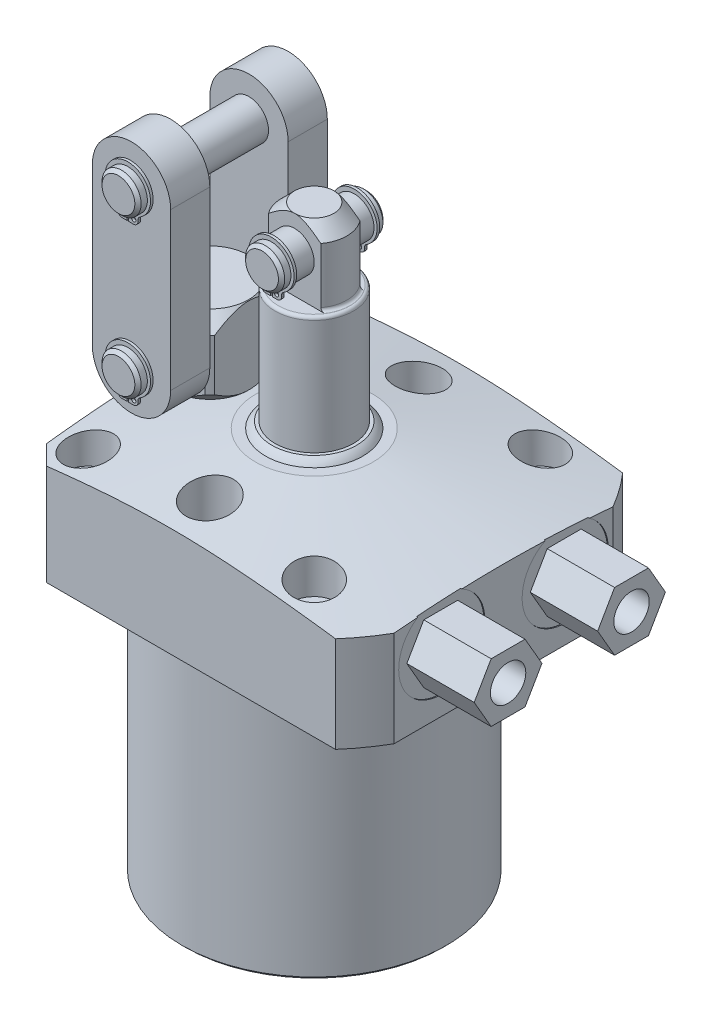
SolidWorks part; units mm, degrees
material "Alloy Steel"
ref_plane "Front Plane" through (0, 0, 0) normal (0, 0, 1) x (1, 0, 0)
ref_plane "Top Plane" through (0, 0, 0) normal (0, 1, 0) x (1, 0, 0)
ref_plane "Right Plane" through (0, 0, 0) normal (1, 0, 0) x (0, 0, -1)
sketch "Sketch28" plane through (0, 0, 0) normal (0, 0, 1) x (1, 0, 0)
  line L0 (0, 0) -> (0, 146.1857) construction
  line L1 (-14.2875, 30.1498) -> (-53.1749, 23.2929)
  line L2 (-53.1749, 23.2929) -> (-53.1749, 0)
  line L3 (-53.1749, 0) -> (-32.1437, 0)
  line L6 (-32.1437, 0) -> (-32.1437, -63.5)
  line L9 (-32.1437, -63.5) -> (0, -63.5)
  line L10 (0, -63.5) -> (0, 30.1498)
  line L11 (0, 30.1498) -> (-14.2875, 30.1498)
  dimension "D2" = 64.2874
  dimension "D3" = 63.5
  dimension "D5" = 106.3498
  dimension "D6" = 10
  dimension "D7" = 28.575
  dimension "D8" = 30.1498
revolve "Revolve7" add sketch "Sketch28" angle 360 about L0
sketch "Sketch3" plane through (0, 30.1498, 0) normal (0, 1, 0) x (-1, 0, 0)
  line L0 (34.925, -34.925) -> (-46.0248, -34.925)
  line L3 (-46.0248, 34.925) -> (34.925, 34.925)
  line L4 (34.925, -34.925) -> (34.925, 34.925)
  line L5 (-46.0248, -34.925) -> (-46.0248, 34.925)
  line L6 (-29.7523, 0) -> (31.3525, 0) construction
  dimension "D1" = 69.85
  dimension "D2" = 46.0248
  dimension "D5" = 34.925
extrude "Cut-Extrude9" cut sketch "Sketch3" against normal up to next (93.6498 mm away) flip side to cut
chamfer "Chamfer8" distance 4.7498 angle 45 2 edges at (-34.925, 11.98, -34.925) (-34.925, 11.98, 34.925)
chamfer "Chamfer5" distance 0.762 angle 45 1 edges at (0, -63.5, -32.1437)
hole_wizard "Hole1" positions "Sketch32" profile "Sketch31" legacy
sketch "Sketch32" plane through (0, 30.1498, 0) normal (0, 1, 0) x (-1, 0, 0)
  line L1 (0, 0) -> (-56.2722, 0) construction
  line L2 (0, 0) -> (0, 46.6984) construction
  point P11 (-27.4955, -27.4955)
  point P23 (-27.4955, 27.4955)
  point P25 (27.4955, -27.4955)
  point P26 (27.4955, 27.4955)
  dimension "D1" = 54.991
  dimension "D2" = 54.991
sketch "Sketch31" plane through (27.4955, 30.1498, -27.4955) normal (1, 0, 0) x (0, 0, 1)
  line L0 (0, 0) -> (0, 30.1498)
  line L1 (0, 30.1498) -> (3.5687, 30.1498)
  line L2 (3.5687, 30.1498) -> (3.5687, 11.9126)
  line L3 (3.5687, 11.9126) -> (5.5499, 11.9126)
  line L4 (5.5499, 11.9126) -> (5.5499, 0)
  line L5 (5.5499, 0) -> (0, 0)
  line L6 (0, 110) -> (0, -10) construction
  dimension "Diameter" = 7.1374
  dimension "Depth" = 30.1498
  dimension "C-Bore Diameter" = 11.0998
  dimension "C-Bore Depth" = 11.9126
sketch "Sketch34" plane through (0, 30.1498, 0) normal (0, 1, 0) x (1, 0, 0)
  line L0 (0, 0) -> (-28.6526, 0) construction
  circle A0 centre (0, 25.4) radius 5.7531
  circle A1 centre (0, -25.4) radius 5.7531
  circle A2 centre (0, 0) radius 25.4 construction
  circle A3 centre (-25.4, 0) radius 5.7531
  dimension "D1" = 11.5062
  dimension "D2" = 25.4
extrude "Cut-Extrude10" cut sketch "Sketch34" against normal blind 15.875
ref_plane "Plane23" through (0, 15.0876, 0) normal (0, -1, 0) x (1, 0, 0)
sketch "S2D0007" plane through (0, 15.0876, 0) normal (0, -1, 0) x (1, 0, 0)
  line L0 (46.0248, -15.0114) -> (46.0248, -25.4889)
  line L1 (46.0248, -25.4889) -> (45.7708, -25.4889)
  line L2 (45.7708, -25.4889) -> (45.7708, -21.228)
  line L3 (45.7708, -21.228) -> (43.7007, -20.788)
  line L4 (43.7007, -20.788) -> (42.9025, -19.9898)
  line L5 (42.9025, -19.9898) -> (31.8008, -19.9898)
  line L6 (31.8008, -19.9898) -> (28.8095, -15.0114)
  line L7 (28.8095, -15.0114) -> (46.0248, -15.0114)
  line L8 (-11.7468, -15.0114) -> (-12.1894, -15.0114) construction
  line L10 (46.0248, -26.6325) -> (46.0248, 26.6325) construction
  dimension "D1" = 12.4333
  dimension "D2" = 59
  dimension "D3" = 9.9568
  dimension "D4" = 45
  dimension "D5" = 12
  dimension "D6" = 2.0701
  dimension "D7" = 0.254
  dimension "D8" = 20.955
  dimension "D9" = 15.0114
  dimension "D10" = 13.97
revolve "Cut-Revolve2" cut sketch "S2D0007" angle 360 about L8
ref_plane "Plane24" through (0, 0, -15.0114) normal (0, 0, 1) x (1, 0, 0)
sketch "Sketch6" plane through (0, 0, -15.0114) normal (0, 0, 1) x (1, 0, 0)
  line L0 (40.0976, 0) -> (-30.1752, 0) construction
  line L1 (45.1675, 0) -> (45.1675, 1.4478)
  line L2 (45.1675, 1.4478) -> (42.1071, 1.4478)
  line L3 (40.0976, 0) -> (46.0248, 0) construction
  line L5 (39.497, 0.5588) -> (40.64, 0.5588)
  line L6 (39.497, 0) -> (45.1675, 0)
  line L8 (39.497, 0.5588) -> (39.497, 0)
  line L9 (39.497, -21.0492) -> (39.497, 0.6686) construction
  arc A1 (40.64, 0.5588) -> (42.1071, 1.4478) centre (39.497, 4.1) ccw
  dimension "D8" = 3.7211
  dimension "D1" = 1.4478
  dimension "D2" = 39.497
  dimension "D7" = 0.5588
  dimension "D9" = 11.3411
  dimension "D10" = 2.286
revolve "Cut-Revolve3" cut sketch "Sketch6" angle 360 about L9
sketch "Sketch38" plane through (45.7708, 0, 0) normal (1, 0, 0) x (0, 0, -1)
  line L1 (23.253, 15.0876) -> (19.1322, 22.225)
  line L2 (19.1322, 22.225) -> (10.8906, 22.225)
  line L3 (10.8906, 22.225) -> (6.7698, 15.0876)
  line L4 (6.7698, 15.0876) -> (10.8906, 7.9502)
  line L5 (10.8906, 7.9502) -> (19.1322, 7.9502)
  line L6 (19.1322, 7.9502) -> (23.253, 15.0876)
  circle A0 centre (15.0114, 15.0876) radius 7.1374 construction
  dimension "D1" = 14.2748
extrude "Extrude14" add sketch "Sketch38" along normal blind 16.383
hole_wizard "Hole2" positions "Sketch40" profile "Sketch39" legacy
sketch "Sketch40" plane through (62.1538, 0, 0) normal (1, 0, 0) x (0, 0, -1)
  arc A0 (10.2098, 24.4001) -> (20.8282, 23.8021) centre (15.0114, 15.0876) ccw construction
  point P0 (15.0114, 15.0876)
sketch "Sketch39" plane through (62.1538, 15.0876, -15.0114) normal (0, 1, 0) x (0, 0, -1)
  line L0 (0, 0) -> (0, 6.7056)
  line L1 (0, 6.7056) -> (4.3053, 6.7056)
  line L2 (4.3053, 6.7056) -> (4.3053, 0)
  line L3 (4.3053, 0) -> (0, 0)
  line L4 (0, 110) -> (0, -10) construction
  dimension "Diameter" = 8.6106
  dimension "Depth" = 6.7056
mirror "Mirror6" about plane through (0, 0, 0) normal (0, 0, 1) of "Hole2", "Extrude14", "Cut-Revolve2", "Cut-Revolve3"
sketch "Sketch33" plane through (0, 0, -15.0114) normal (0, 0, 1) x (1, 0, 0)
  line L0 (39.497, 8.3297) -> (39.497, -4.9597) construction
  line L1 (39.497, 2.4904) -> (39.497, -1.971) construction
  line L2 (33.8264, 1.4478) -> (45.1675, 1.4478) construction
  circle A0 centre (34.7154, 0.5842) radius 0.889
  dimension "D3" = 1.778
  dimension "D1" = 9.5631
  dimension "D2" = 0.8636
revolve "Revolve9" add sketch "Sketch33" angle 360 about L0
mirror "Mirror7" about plane through (0, 0, 0) normal (0, 0, 1) of bodies 147
sketch "Sketch12" plane through (0, 0, 0) normal (0, 0, -1) x (-1, 0, 0)
  line L0 (0, 30.1498) -> (0, 31.6738)
  line L1 (0, 31.6738) -> (10.287, 31.6738)
  line L2 (0, 30.1498) -> (11.811, 30.1498)
  line L3 (0, 22.1056) -> (0, 27.6194) construction
  line L4 (14.2875, 30.1498) -> (-14.2875, 30.1498) construction
  arc A0 (11.811, 30.1498) -> (10.287, 31.6738) centre (7.778, 27.6408) ccw
  dimension "D1" = 4.7498
  dimension "D2" = 1.524
  dimension "D3" = 20.574
  dimension "D4" = 23.622
revolve "Revolve2" add sketch "Sketch12" angle 360 about L3
ref_plane "Plane25" through (0, 0, 0) normal (0, 0, 1) x (1, 0, 0)
sketch "Sketch13" plane through (0, 0, 0) normal (0, 0, 1) x (1, 0, 0)
  line L0 (0, 31.6738) -> (0, 77.7748)
  line L1 (0, 77.7748) -> (4.7625, 77.7748)
  line L2 (4.7625, 77.7748) -> (7.9375, 74.5998)
  line L3 (7.9375, 60.325) -> (7.9375, 74.5998)
  line L4 (9.5187, 31.6738) -> (0, 31.6738)
  line L5 (0, 23.0264) -> (0, 64.961) construction
  line L6 (-6.0362, 69.85) -> (17.7755, 69.85) construction
  line L7 (10.287, 31.6738) -> (-10.287, 31.6738) construction
  line L8 (40.0976, 0) -> (-30.1752, 0) construction
  line L10 (7.9375, 60.325) -> (9.5187, 60.325)
  line L11 (9.5187, 60.325) -> (9.5187, 31.6738)
  dimension "D1" = 7.9248
  dimension "D2" = 69.85
  dimension "D3" = 15.875
  dimension "D4" = 45
  dimension "D5" = 3.175
  dimension "D6" = 19.0373
  dimension "D7" = 17.4498
revolve "Revolve3" add sketch "Sketch13" angle 360 about L5
sketch "Sketch14" plane through (0, 77.7748, 0) normal (0, 1, 0) x (-1, 0, 0)
  line L0 (-6.35, 4.7625) -> (6.35, 4.7625)
  line L2 (6.35, -4.7625) -> (-6.35, -4.7625)
  line L4 (0, 0) -> (-0.0001, 0) construction
  line L5 (34.2265, 0) -> (-34.2265, 0) construction
  circle A0 centre (0, 0) radius 7.9375 construction
  arc A1 (6.35, 4.7625) -> (-6.35, 4.7625) centre (0, 0) ccw
  arc A2 (-6.35, -4.7625) -> (6.35, -4.7625) centre (0, 0) ccw
  dimension "D1" = 9.525
extrude "Cut-Extrude7" cut sketch "Sketch14" against normal up to surface (17.4498 mm away) up to face at (0, 60.325, -7.9375)
fillet "Fillet4" radius 0.762 3 edges at (0, 60.325, -9.5187) (-7.9375, 60.325, 0) (7.9375, 60.325, 0)
sketch "Sketch29" plane through (0, 0, 0) normal (0, 0, 1) x (1, 0, 0)
  line L0 (0, 77.7748) -> (-4.7625, 77.7748) construction
  circle A0 centre (0, 69.85) radius 4.7523
  dimension "D1" = 9.5047
  dimension "D2" = 7.9248
extrude "Extrude11" add sketch "Sketch29" along normal mid plane 25.4
sketch "Sketch16" plane through (0, 52.3748, 12.7) normal (0, 0, 1) x (1, 0, 0)
  line L0 (0.2083, 13.0097) -> (0.2083, 10.7745)
  line L1 (2.4435, 12.1667) -> (2.4435, 11.8159)
  line L2 (1.4021, 10.7745) -> (0.2083, 10.7745)
  line L3 (-2.4435, 12.1667) -> (-2.4435, 11.8159)
  line L4 (-1.4021, 10.7745) -> (-0.2083, 10.7745)
  line L5 (-0.2083, 13.0097) -> (-0.2083, 10.7745)
  line L6 (0, -3.8062) -> (0, 3.1748) construction
  arc A0 (0.2083, 13.0097) -> (-0.2083, 13.0097) centre (0, 17.4752) ccw
  arc A1 (2.9311, 13.0487) -> (-2.9311, 13.0487) centre (0, 17.7165) ccw
  arc A2 (2.9311, 13.0487) -> (2.4435, 12.1667) centre (3.4849, 12.1667) ccw
  arc A3 (1.4021, 10.7745) -> (2.4435, 11.8159) centre (1.4021, 11.8159) ccw
  circle A4 centre (1.2446, 11.8159) radius 0.5207
  arc A5 (-2.9311, 13.0487) -> (-2.4435, 12.1667) centre (-3.4849, 12.1667) cw
  arc A6 (-1.4021, 10.7745) -> (-2.4435, 11.8159) centre (-1.4021, 11.8159) cw
  circle A7 centre (-1.2446, 11.8159) radius 0.5207
  circle A8 centre (0, 17.4752) radius 4.7523 construction
  dimension "D1" = 5.5118
  dimension "D4" = 1.0414
  dimension "D6" = 1.0414
  dimension "D7" = 2.2352
  dimension "D8" = 4.4704
  dimension "D10" = 1.0414
  dimension "D11" = 1.0414
  dimension "D2" = 2.2352
  dimension "D3" = 0.2413
  dimension "D5" = 1.2446
  dimension "D9" = 0.4166
extrude "Extrude2" add sketch "Sketch16" against normal blind 0.635 from offset 2.286
chamfer "Chamfer6" distance 0.762 angle 45 2 edges at (4.7523, 69.85, -12.7) (4.7523, 69.85, 12.7)
mirror "Mirror2" about plane through (0, 0, 0) normal (0, 0, 1) of "Extrude2"
sketch "Sketch35" plane through (0, 0, 0) normal (0, 0, 1) x (1, 0, 0)
  line L0 (-25.4, 43.5741) -> (-25.4, 11.6793) construction
  line L1 (-25.4, 14.2748) -> (-19.05, 14.2748)
  line L2 (-19.05, 14.2748) -> (-19.05, 30.1498)
  line L3 (-19.05, 30.1498) -> (-16.002, 30.1498)
  line L4 (-12.7, 33.4518) -> (-12.7, 45.8978)
  line L5 (-16.002, 49.1998) -> (-25.4, 49.1998)
  line L6 (-25.4, 49.1998) -> (-25.4, 14.2748)
  line L8 (-12.7, 45.8978) -> (-16.002, 49.1998)
  line L9 (-16.002, 30.1498) -> (-12.7, 33.4518)
  line L10 (40.0976, 0) -> (46.0248, 0) construction
  point P6 (-12.7, 30.1498)
  point P7 (-12.7, 49.1998)
  dimension "D2" = 12.7
  dimension "D3" = 25.4
  dimension "D4" = 34.925
  dimension "D5" = 19.05
  dimension "D6" = 25.4
  dimension "D9" = 3.302
  dimension "D10" = 3.302
  dimension "D7" = 30.1498
revolve "Revolve10" add sketch "Sketch35" angle 360 about L0
sketch "Sketch36" plane through (0, 49.1998, 0) normal (0, 1, 0) x (1, 0, 0)
  line L0 (-25.4, 0) -> (-25.4, 48.7489) construction
  line L1 (-33.8003, 9.525) -> (-16.9997, 9.525)
  line L2 (-34.925, 8.4003) -> (-34.925, -8.4003)
  line L3 (-33.8003, -9.525) -> (-16.9997, -9.525)
  line L4 (-15.875, 8.4003) -> (-15.875, -8.4003)
  line L5 (-25.4, 0) -> (0, 0) construction
  line L6 (-34.2265, 0) -> (34.2265, 0) construction
  circle A0 centre (-25.4, 0) radius 12.7 construction
  arc A2 (-34.925, 8.4003) -> (-34.925, -8.4003) centre (-25.4, 0) ccw
  arc A3 (-33.8003, -9.525) -> (-16.9997, -9.525) centre (-25.4, 0) ccw
  arc A4 (-16.9997, 9.525) -> (-33.8003, 9.525) centre (-25.4, 0) ccw
  arc A5 (-15.875, -8.4003) -> (-15.875, 8.4003) centre (-25.4, 0) ccw
  dimension "D1" = 19.05
  dimension "D2" = 19.05
extrude "Cut-Extrude11" cut sketch "Sketch36" against normal up to surface (19.05 mm away) up to face at (-34.798, 30.1498, 0)
sketch "Sketch30" plane through (0, 0, 0) normal (0, 0, 1) x (1, 0, 0)
  line L0 (-53.1749, 0) -> (-40.0976, 0) construction
  circle A0 centre (-25.4, 39.6748) radius 4.7523
  dimension "D3" = 9.5047
  dimension "D1" = 39.6748
  dimension "D2" = 25.4
extrude "Extrude12" add sketch "Sketch30" along normal mid plane 44.45
sketch "Sketch19" plane through (-22.225, 11.0998, 22.225) normal (0, 0, 1) x (1, 0, 0)
  line L0 (-2.9667, 24.1095) -> (-2.9667, 21.8743)
  line L1 (-0.7315, 23.2665) -> (-0.7315, 22.9157)
  line L2 (-1.7729, 21.8743) -> (-2.9667, 21.8743)
  line L3 (-5.6185, 23.2665) -> (-5.6185, 22.9157)
  line L4 (-4.5771, 21.8743) -> (-3.3833, 21.8743)
  line L5 (-3.3833, 24.1095) -> (-3.3833, 21.8743)
  line L6 (-3.175, -5.3833) -> (-3.175, 4.2478) construction
  arc A0 (-2.9667, 24.1095) -> (-3.3833, 24.1095) centre (-3.175, 28.575) ccw
  arc A1 (-0.2439, 24.1485) -> (-6.1061, 24.1485) centre (-3.175, 28.8163) ccw
  arc A2 (-0.2439, 24.1485) -> (-0.7315, 23.2665) centre (0.3099, 23.2665) ccw
  arc A3 (-1.7729, 21.8743) -> (-0.7315, 22.9157) centre (-1.7729, 22.9157) ccw
  circle A4 centre (-1.7221, 22.9157) radius 0.5207
  arc A5 (-6.1061, 24.1485) -> (-5.6185, 23.2665) centre (-6.6599, 23.2665) cw
  arc A6 (-4.5771, 21.8743) -> (-5.6185, 22.9157) centre (-4.5771, 22.9157) cw
  circle A7 centre (-4.6279, 22.9157) radius 0.5207
  circle A8 centre (-3.175, 28.575) radius 4.7523 construction
  dimension "D1" = 5.5118
  dimension "D3" = 0.2413
  dimension "D4" = 1.0414
  dimension "D5" = 1.0414
  dimension "D6" = 1.0414
  dimension "D9" = 4.4704
  dimension "D2" = 2.2352
  dimension "D7" = 0.4166
  dimension "D8" = 2.2352
  dimension "D10" = 1.0414
  dimension "D11" = 1.2446
extrude "Extrude4" add sketch "Sketch19" against normal blind 0.635 from offset 2.286
sketch "Sketch37" plane through (0, 0, 9.525) normal (0, 0, 1) x (1, 0, 0)
  line L0 (-34.925, 77.7748) -> (-34.925, 39.6748)
  line L1 (-15.875, 77.7748) -> (-15.875, 39.6748)
  arc A0 (-15.875, 77.7748) -> (-34.925, 77.7748) centre (-25.4, 77.7748) ccw
  arc A1 (-34.925, 39.6748) -> (-15.875, 39.6748) centre (-25.4, 39.6748) ccw
  dimension "D1" = 19.05
  dimension "D2" = 38.1
  dimension "D3" = 26.6076
extrude "Extrude13" add sketch "Sketch37" along normal blind 9.525
mirror "Mirror3" about plane through (0, 0, 0) normal (0, 0, 1) of "Extrude4"
chamfer "Chamfer7" distance 0.762 angle 45 2 edges at (-20.6477, 39.6748, -22.225) (-20.6477, 39.6748, 22.225)
pattern_linear "LPattern2" count 2 spacing 38.1 along (0, 1, 0) of "Extrude4", "Mirror3", "Chamfer7", "Extrude12"
mirror "Mirror8" about plane through (0, 0, 0) normal (0, 0, 1) of "Extrude13"
